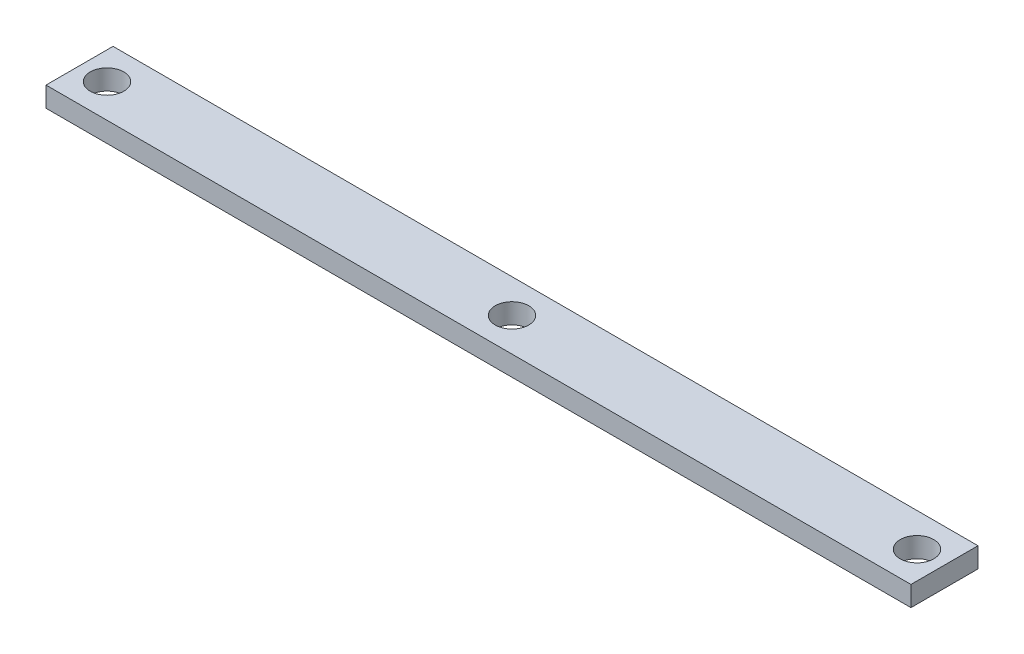
SolidWorks part; units mm, degrees
ref_plane "Front Plane" through (0, 0, 0) normal (0, 0, 1) x (1, 0, 0)
ref_plane "Top Plane" through (0, 0, 0) normal (0, 1, 0) x (1, 0, 0)
ref_plane "Right Plane" through (0, 0, 0) normal (1, 0, 0) x (0, 0, -1)
sketch "Sketch1" plane through (0, 0, 0) normal (0, 0, 1) x (1, 0, 0)
  line L0 (0, 0) -> (0, 3)
  line L1 (0, 3) -> (129, 3)
  line L2 (129, 3) -> (129, 0)
  line L3 (0, 0) -> (129, 0)
  dimension "D4" = 3
  dimension "D5" = 129
extrude "Boss-Extrude1" add sketch "Sketch1" along normal blind 10
sketch "Sketch2" plane through (0, 0, 0) normal (0, -1, 0) x (1, 0, 0)
  line L0 (0, 10) -> (129, 10) construction
  line L1 (0, 0) -> (129, 10) construction
  line L3 (129, 10) -> (129, 0) construction
  circle A0 centre (4.1, 5) radius 2.5
  circle A1 centre (64.5, 5) radius 2.5
  circle A2 centre (124.9, 5) radius 2.5
  dimension "D1" = 5
  dimension "D2" = 60.4
  dimension "D3" = 60.4
extrude "Cut-Extrude1" cut sketch "Sketch2" against normal through all
sketch "Sketch3" plane through (0, 0, 0) normal (0, 1, 0) x (1, 0, 0)
  line L0 (13.5, -2.4) -> (13.5, -3.4) construction
  line L1 (10, -2.4) -> (17, -2.4)
  line L2 (10, -2.4) -> (10, -3.4)
  line L3 (10, -3.4) -> (17, -3.4)
  line L4 (17, -2.4) -> (17, -3.4)
  line L5 (10, -6.6) -> (17, -6.6)
  line L6 (10, -6.6) -> (10, -7.6)
  line L7 (10, -7.6) -> (17, -7.6)
  line L8 (17, -6.6) -> (17, -7.6)
  line L9 (13.5, -6.6) -> (13.5, -7.6) construction
  line L10 (10, -3.4) -> (10, -6.6) construction
  line L11 (10, -5) -> (4.1, -5) construction
  line L12 (79.5, -2.4) -> (79.5, -3.4) construction
  line L13 (76, -2.4) -> (83, -2.4)
  line L14 (76, -2.4) -> (76, -3.4)
  line L15 (76, -3.4) -> (83, -3.4)
  line L16 (83, -2.4) -> (83, -3.4)
  line L17 (76, -6.6) -> (83, -6.6)
  line L18 (76, -6.6) -> (76, -7.6)
  line L19 (76, -7.6) -> (83, -7.6)
  line L20 (83, -6.6) -> (83, -7.6)
  circle A0 centre (64.5, -5) radius 2.5 construction
  dimension "D1" = 3.2
  dimension "D2" = 1
  dimension "D3" = 7
  dimension "D4" = 51
  dimension "D5" = 15
extrude "Boss-Extrude2" add sketch "Sketch3" against normal blind 2
fillet "Fillet1" radius 1 8 edges at (79.5, 0, 3.4) (79.5, 0, 7.6) (13.5, 0, 7.6) (13.5, 0, 3.4) (79.5, 0, 6.6) (79.5, 0, 2.4) (13.5, 0, 6.6) (13.5, 0, 2.4)
pattern_linear "LPattern1" count 4 spacing 12 along (1, 0, 0) of "Boss-Extrude2", "Fillet1"
